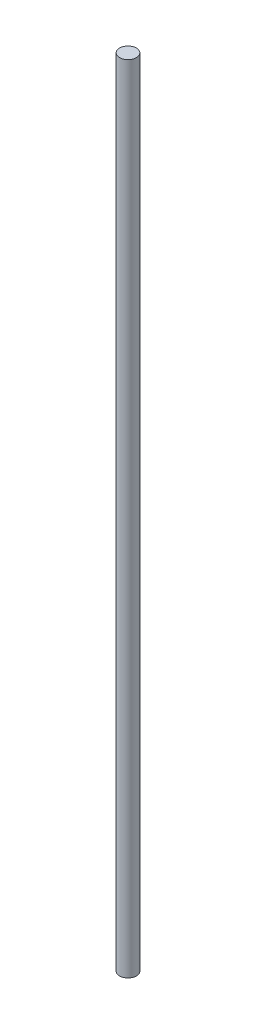
SolidWorks part; units mm, degrees
ref_plane "Front Plane" through (0, 0, 0) normal (0, 0, 1) x (1, 0, 0)
ref_plane "Top Plane" through (0, 0, 0) normal (0, 1, 0) x (1, 0, 0)
ref_plane "Right Plane" through (0, 0, 0) normal (1, 0, 0) x (0, 0, -1)
sketch "Sketch1" plane through (0, 0, 0) normal (0, 1, 0) x (1, 0, 0)
  circle A0 centre (0, 0) radius 4
  dimension "D1" = 8
extrude "Boss-Extrude1" add sketch "Sketch1" along normal blind 380
cosmetic thread "Cosmetic Thread1"
